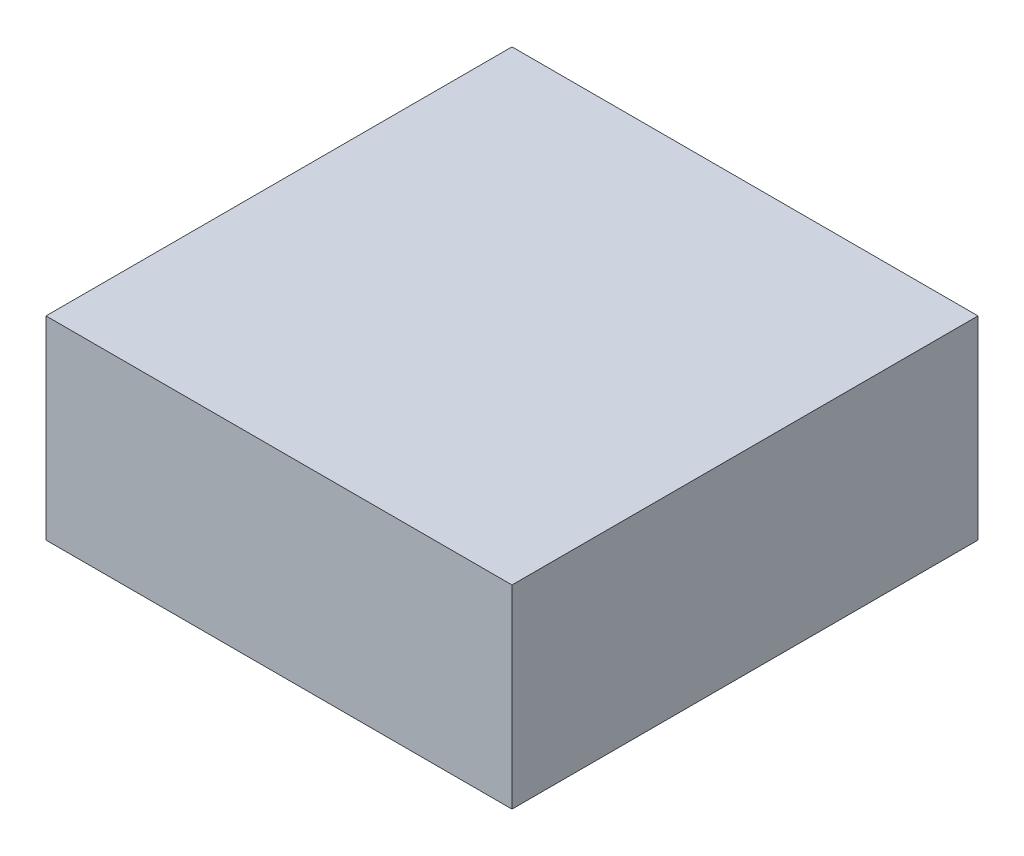
SolidWorks part; units mm, degrees
material "Polypropylene"
ref_plane "Front Plane" through (0, 0, 0) normal (0, 0, 1) x (1, 0, 0)
ref_plane "Top Plane" through (0, 0, 0) normal (0, 1, 0) x (1, 0, 0)
ref_plane "Right Plane" through (0, 0, 0) normal (1, 0, 0) x (0, 0, -1)
sketch "Sketch1" plane through (0, 0, 0) normal (0, 1, 0) x (1, 0, 0)
  line L1 (-600, -600) -> (600, -600)
  line L2 (-600, -600) -> (-600, 600)
  line L3 (-600, 600) -> (600, 600)
  line L4 (600, -600) -> (600, 600)
  line L5 (-600, -600) -> (600, 600) construction
  line L6 (-600, 600) -> (600, -600) construction
  point P0 (0, 0)
  dimension "D1" = 1200
  dimension "D2" = 1200
extrude "Boss-Extrude1" add sketch "Sketch1" along normal blind 500
